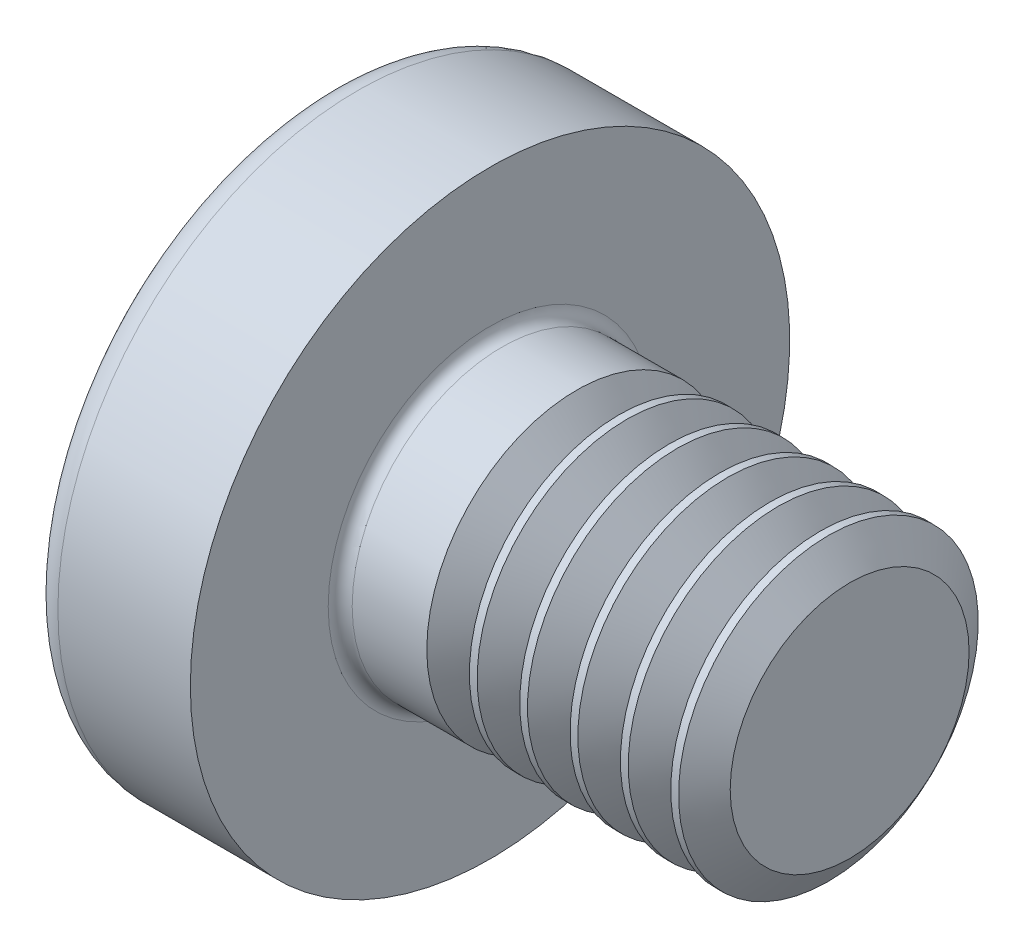
SolidWorks part; units mm, degrees
ref_plane "Plane1" through (0, 0, 0) normal (0, 0, 1) x (1, 0, 0)
ref_plane "Plane2" through (0, 0, 0) normal (0, 1, 0) x (1, 0, 0)
ref_plane "Plane3" through (0, 0, 0) normal (1, 0, 0) x (0, 0, -1)
sketch "BodySke" plane through (0, 0, 0) normal (0, 0, 1) x (1, 0, 0)
  line L0 (2.1, 1.25) -> (2.1, 2.5)
  line L1 (2.325, 6.35) -> (2.325, -3.175) construction
  line L2 (-25.4, 0) -> (127, 0) construction
  line L3 (5.1, 0) -> (0, 0)
  line L4 (2.1, 1.25) -> (5.1, 1.25)
  line L5 (5.1, 1.25) -> (5.1, 0)
  line L6 (0.995, 2.5) -> (2.1, 2.5)
  line L8 (2.1, 6.35) -> (2.1, -3.175) construction
  arc A0 (0.8032, 2.4043) -> (0, 0) centre (4, 0) ccw
  arc A2 (0.8032, 2.4043) -> (0.995, 2.5) centre (0.995, 2.26) cw
revolve "Base-Revolve" add sketch "BodySke"
cosmetic thread "ThreadCosmetic" [suppressed]
fillet "Fillet1" radius 0.1 1 edges at (2.1, 0, 1.25)
sketch "Sketch3" plane through (0, 0, 0) normal (1, 0, 0) x (0, 0, -1)
  line L0 (0.37, -1.3) -> (-0.37, -1.3)
  line L1 (0.37, -1.3) -> (0.37, 1.3)
  line L2 (-0.37, 1.3) -> (0.37, 1.3)
  line L3 (-0.37, 1.3) -> (-0.37, -1.3)
ref_plane "Plane4" through (1.5, 0, 0) normal (1, 0, 0) x (0, 0, -1)
sketch "Sketch4" plane through (1.5, 0, 0) normal (1, 0, 0) x (0, 0, -1)
  line L0 (0.37, -0.5521) -> (-0.37, -0.5521)
  line L1 (0.37, -0.5521) -> (0.37, 0.5521)
  line L2 (-0.37, 0.5521) -> (0.37, 0.5521)
  line L3 (-0.37, 0.5521) -> (-0.37, -0.5521)
loft "Recess" cut profiles "Sketch3", "Sketch4"
pattern_circular "RecPat" count 2 every 90 about axis through (0, 0, 0) along (1, 0, 0) of "Recess"
sketch "RecCorSke" plane through (0, 0, 0) normal (0, 0, 1) x (1, 0, 0)
  line L0 (-3.175, 0) -> (15.875, 0) construction
  line L1 (-25.4, 0) -> (127, 0) construction
  line L2 (0, 0) -> (0, 0.6609)
  line L3 (0, 0.6609) -> (1.5, 0.556)
  line L4 (1.5, 0.556) -> (1.6807, 0)
  line L5 (1.6807, 0) -> (0, 0)
revolve "RecessCore" cut sketch "RecCorSke" angle 360 about L0
sketch "ThdSchSke" plane through (0, 0, 0) normal (0, 0, 1) x (1, 0, 0)
  line L0 (3, -0.9965) -> (2.8225, -1.25)
  line L1 (3, -0.9965) -> (3.1775, -1.25)
  line L2 (3.1775, -1.25) -> (3.1775, -1.5625)
  line L3 (-3.175, 0) -> (5.1513, 0) construction
  line L5 (3.1775, -1.5625) -> (2.8225, -1.5625)
  line L6 (2.8225, -1.5625) -> (2.8225, -1.25)
revolve "ThreadSchematic" cut sketch "ThdSchSke" angle 360 about L3
pattern_linear "ThdSchPat" count 6 spacing 0.42 along (1, 0, 0) of "ThreadSchematic"
equation "\"D1@Sketch3\" = \"Cross_dia@Sketch3\" / 2"
equation "\"D2@Sketch3\" = \"Cross_width@Sketch3\" / 2"
equation "\"Depth@RecCorSke\" = \"Cross_depth@Plane4\""
equation "\"D1@Sketch4\" = \"Cross_width@Sketch3\""
equation "\"D2@Sketch4\" = \"Cross_dia@Sketch3\" - 2.0 * \"Cross_depth@Plane4\" * tan(26.5  * 0.017453292)"
equation "\"D3@Sketch4\" = \"D1@Sketch4\" / 2"
equation "\"D4@Sketch4\" = \"D2@Sketch4\" / 2"
equation "\"Thread_length@ThreadCosmetic\" = ((sgn( (\"Length@BodySke\" - \"Advance@BodySke\" * 2.0 ) - \"Thread_nom@BodySke\" )-1)*( (\"Length@BodySke\" - \"Advance@BodySke\" * 2.0 ) - \"Thread_nom@BodySke\" ))/-2+ \"Thread_nom@BodySke\""
equation "\"Thread_minor@ThdSchSke\" = \"Thread_minor@ThreadCosmetic\""
equation "\"Diameter@ThdSchSke\" = \"Diameter@BodySke\""
equation "\"Overcut@ThdSchSke\" = \"Diameter@BodySke\" * 1.25"
equation "\"Start@ThdSchSke\" = \"Head_ht@BodySke\" + \"Length@BodySke\" - \"Thread_length@ThreadCosmetic\"  '---Non-countersunk---"
equation "\"Num_threads@ThdSchPat\" = int( \"Thread_length@ThreadCosmetic\" / \"Advance@BodySke\" + 0.999 )  + 1"
equation "\"Advance@ThdSchPat\" = \"Thread_length@ThreadCosmetic\" /  (\"Num_threads@ThdSchPat\" - 1) 'relax it"
